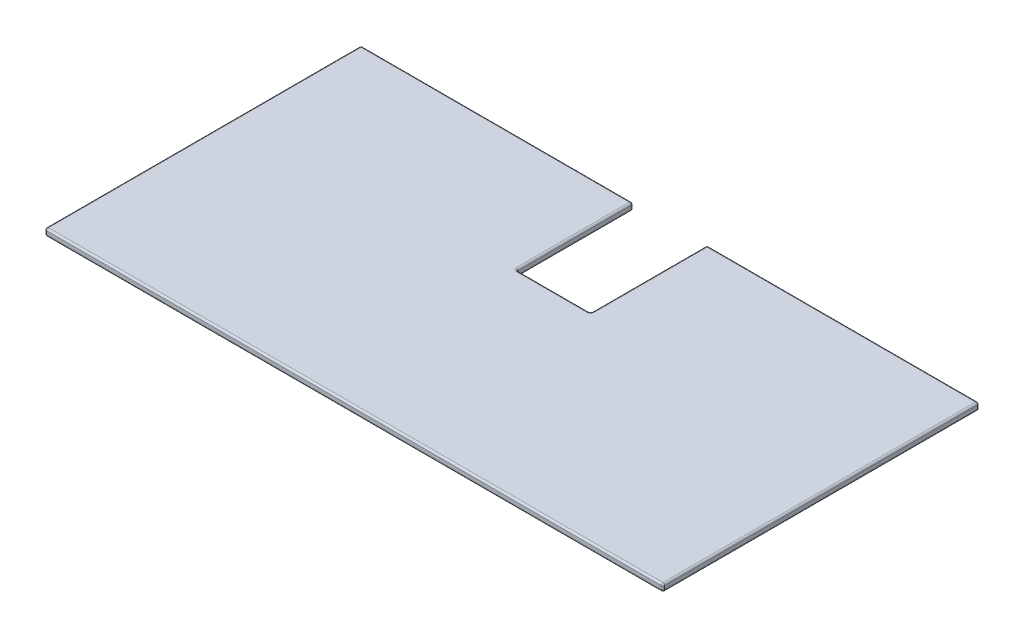
SolidWorks part; units mm, degrees
material "1060 Alloy"
ref_plane "Front Plane" through (0, 0, 0) normal (0, 0, 1) x (1, 0, 0)
ref_plane "Top Plane" through (0, 0, 0) normal (0, 1, 0) x (1, 0, 0)
ref_plane "Right Plane" through (0, 0, 0) normal (1, 0, 0) x (0, 0, -1)
sketch "Sketch1" plane through (0, 0, 0) normal (0, 1, 0) x (1, 0, 0)
  line L1 (-875, 447.5) -> (875, 447.5)
  line L2 (-875, 447.5) -> (-875, -447.5)
  line L3 (-875, -447.5) -> (875, -447.5)
  line L4 (875, 447.5) -> (875, -447.5)
  line L5 (-875, 447.5) -> (875, -447.5) construction
  line L6 (-875, -447.5) -> (875, 447.5) construction
  point P0 (0, 0)
  dimension "D1" = 895
  dimension "D2" = 1750
extrude "Boss-Extrude1" add sketch "Sketch1" along normal blind 20
sketch "Sketch2" plane through (0, 20, 0) normal (0, 1, 0) x (1, 0, 0)
  line L0 (875, 447.5) -> (-875, 447.5) construction
  line L1 (-105, 777.5) -> (105, 777.5)
  line L2 (-105, 777.5) -> (-105, 117.5)
  line L3 (-105, 117.5) -> (105, 117.5)
  line L4 (105, 777.5) -> (105, 117.5)
  line L5 (-105, 777.5) -> (105, 117.5) construction
  line L6 (-105, 117.5) -> (105, 777.5) construction
  point P0 (0, 447.5)
  dimension "D1" = 210
  dimension "D2" = 660
extrude "Cut-Extrude1" cut sketch "Sketch2" against normal blind 20
fillet "Fillet1" radius 5 24 edges at (105, 20, -282.5) (-105, 20, -282.5) (0, 20, -117.5) (875, 20, 0) (-490, 20, -447.5) (490, 20, -447.5) (-875, 20, 0) (0, 20, 447.5) (-105, 0, -282.5) (875, 10, -447.5) (-875, 10, -447.5) (-875, 10, 447.5) (875, 10, 447.5) (0, 0, 447.5) (-875, 0, 0) (490, 0, -447.5) (-490, 0, -447.5) (875, 0, 0) (105, 10, -447.5) (-105, 10, -447.5) (105, 10, -117.5) (-105, 10, -117.5) (0, 0, -117.5) (105, 0, -282.5)
